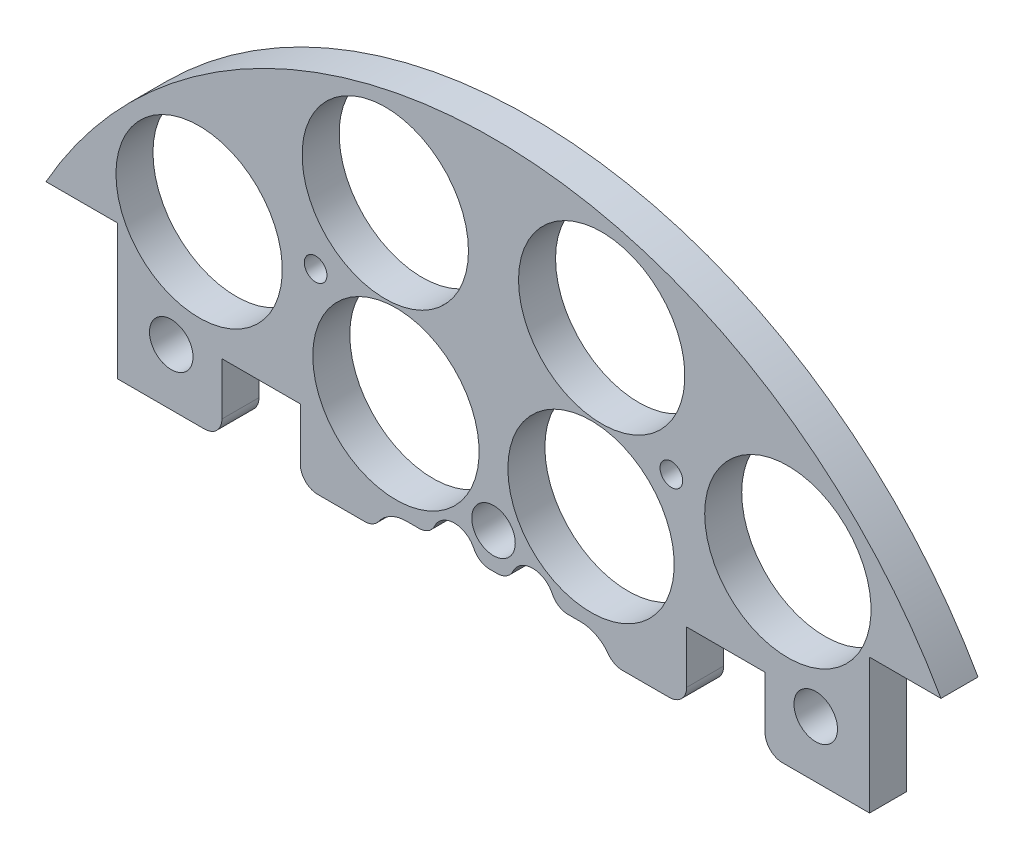
SolidWorks part; units mm, degrees
ref_plane "Front Plane" through (0, 0, 0) normal (0, 0, 1) x (1, 0, 0)
ref_plane "Top Plane" through (0, 0, 0) normal (0, 1, 0) x (1, 0, 0)
ref_plane "Right Plane" through (0, 0, 0) normal (1, 0, 0) x (0, 0, -1)
sketch "Sketch1" plane through (0, 0, 0) normal (0, 0, 1) x (1, 0, 0)
  line L0 (0, 0) -> (-82.1241, 0) construction
  line L1 (0, 0) -> (0, 95.6219) construction
  line L3 (-65.2538, 36.83) -> (-54.8398, 36.83)
  line L5 (-65.2538, -36.83) -> (-54.8398, -36.83)
  line L6 (-54.8398, 36.83) -> (-54.8398, -36.83)
  line L7 (65.2538, -36.83) -> (54.8398, -36.83)
  line L8 (65.2538, 36.83) -> (54.8398, 36.83)
  line L9 (54.8398, 36.83) -> (54.8398, -36.83)
  arc A0 (-65.2538, -36.83) -> (65.2538, -36.83) centre (0, 0) ccw
  circle A1 centre (-45.466, 11.049) radius 1.651
  circle A2 centre (-20.0673, 10.795) radius 1.651
  circle A3 centre (-20.0673, -10.795) radius 1.651
  circle A4 centre (-45.466, -11.049) radius 1.651
  circle A5 centre (45.466, -11.049) radius 1.651
  circle A6 centre (20.0673, -10.795) radius 1.651
  circle A7 centre (20.0673, 10.795) radius 1.651
  circle A8 centre (45.466, 11.049) radius 1.651
  arc A9 (65.2538, 36.83) -> (-65.2538, 36.83) centre (0, 0) ccw
  dimension "D2" = 3.302
  dimension "D3" = 3.302
  dimension "D4" = 25.4
  dimension "D5" = 10.795
  dimension "D10" = 45.466
  dimension "D6" = 73.66
  dimension "D7" = 10.414
  dimension "D8" = 74.93
  dimension "D9" = 74.93
  dimension "D11" = 36.83
extrude "Boss-Extrude2" add sketch "Sketch1" along normal blind 5.3975
sketch "Sketch2" plane through (0, 0, 5.3975) normal (0, 0, 1) x (1, 0, 0)
  line L0 (0, 68.58) -> (0, 55.88) construction
  line L1 (-9.525, 68.58) -> (9.525, 68.58)
  line L2 (-9.525, 68.58) -> (-9.525, 55.88)
  line L3 (-9.525, 55.88) -> (9.525, 55.88)
  line L4 (9.525, 68.58) -> (9.525, 55.88)
  line L5 (-9.525, 62.23) -> (9.525, 62.23) construction
  arc A0 (65.2538, 36.83) -> (-65.2538, 36.83) centre (0, 0) ccw construction
  circle A1 centre (-20.0673, 10.795) radius 1.651 construction
  circle A2 centre (20.0673, 10.795) radius 1.651 construction
  circle A3 centre (-6.731, 62.23) radius 1.143
  circle A4 centre (6.731, 62.23) radius 1.143
  dimension "D4" = 2.286
  dimension "D5" = 0
  dimension "D6" = 6.731
  dimension "D1" = 19.05
  dimension "D2" = 12.7
  dimension "D3" = 55.88
extrude "Cut-Extrude1" cut sketch "Sketch2" against normal through all contours A3 | A4
sketch "Sketch3" plane through (0, 0, 0) normal (0, 0, -1) x (-1, 0, 0)
  line L0 (0, 0) -> (0, -116.2908) construction
  line L1 (0, 0) -> (-153.8039, 0) construction
  circle A0 centre (-14.224, -56.7251) radius 12.1285
  circle A3 centre (14.224, -56.7251) radius 12.1285
  circle A4 centre (-42.926, -42.926) radius 12.1285
  circle A5 centre (14.224, 34.29) radius 12.1285
  circle A6 centre (-14.224, 34.29) radius 12.1285
  circle A8 centre (-42.926, 42.926) radius 12.1285
  circle A11 centre (42.926, 42.926) radius 12.1285
  circle A14 centre (42.926, -42.926) radius 12.1285
  point P36 (0, 0)
  point P53 (0, 0)
  point P55 (0, 0)
  dimension "D1" = 34.29
  dimension "D2" = 14.224
  dimension "D3" = 24.257
  dimension "D4" = 42.926
  dimension "D5" = 42.926
extrude "Cut-Extrude2" cut sketch "Sketch3" against normal through all
sketch "Sketch4" plane through (0, 0, 0) normal (0, 0, -1) x (-1, 0, 0)
  line L1 (-15.7702, 56.3138) -> (12.7925, 56.3138)
  line L2 (-15.7702, 56.3138) -> (-15.7702, 67.9913)
  line L3 (-15.7702, 67.9913) -> (12.7925, 67.9913)
  line L4 (12.7925, 56.3138) -> (12.7925, 67.9913)
extrude "Boss-Extrude3" add sketch "Sketch4" against normal up to surface (5.3975 mm away) up to face at (-55.0545, -42.926, 5.3975)
sketch "Sketch5" plane through (0, 0, 0) normal (0, 0, -1) x (-1, 0, 0)
  line L1 (-113.3786, -90.442) -> (117.3207, -90.442)
  line L2 (-113.3786, -90.442) -> (-113.3786, 17.145)
  line L3 (-113.3786, 17.145) -> (117.3207, 17.145)
  line L4 (117.3207, -90.442) -> (117.3207, 17.145)
  circle A1 centre (20.0673, 10.795) radius 1.651 construction
  dimension "D1" = 6.35
extrude "Cut-Extrude3" cut sketch "Sketch5" against normal through all
sketch "Sketch6" plane through (0, 0, 0) normal (0, 0, -1) x (-1, 0, 0)
  line L0 (0, 0) -> (0, 74.93) construction
  line L1 (0, 0) -> (-15.5068, 57.8721) construction
  arc A0 (65.2538, 36.83) -> (-65.2538, 36.83) centre (0, 0) ccw construction
  circle A1 centre (-15.7776, 58.8828) radius 12.1285
  circle A3 centre (15.7776, 58.8828) radius 12.1285
  dimension "D1" = 24.257
  dimension "D2" = 0
  dimension "D4" = 60.96
  dimension "D3" = 15
extrude "Cut-Extrude4" cut sketch "Sketch6" against normal through all
extrude "Cut-Extrude55" cut sketch "Sketch57" against normal through all both and the other way through all
sketch "Sketch57" plane through (-29.8755, 133.1307, 31.75) normal (0, 0, 1) x (0.01, 0.9999, 0)
  line L0 (-132.559, -31.3134) -> (-132.559, 57.8454) construction
  line L1 (-132.559, -31.3134) -> (-222.516, -31.3134) construction
  circle A0 centre (-157.959, 14.4066) radius 3.175
  circle A1 centre (-173.199, -31.3134) radius 3.175
  circle A3 centre (-157.959, -77.0334) radius 3.175
  circle A4 centre (-107.159, -77.0334) radius 3.175
  circle A5 centre (-91.919, -31.3134) radius 3.175
  circle A6 centre (-107.159, 14.4066) radius 3.175
sketch "Sketch58" [suppressed] plane through (0, 0, 0) normal (0, 0, -1) x (-1, 0, 0)
  circle A0 centre (-46.0825, 25.2068) radius 4.445
  circle A1 centre (-0.5172, 40.9032) radius 4.445
  circle A2 centre (45.3529, 26.1212) radius 4.445
  circle A3 centre (-46.0825, 25.2068) radius 3.175 construction
  circle A4 centre (-0.5172, 40.9032) radius 3.175 construction
  circle A5 centre (45.3529, 26.1212) radius 3.175 construction
  dimension "D1" = 1.27
  dimension "D2" = 1.27
  dimension "D3" = 1.27
extrude "Boss-Extrude4" [suppressed] add sketch "Sketch58" against normal up to surface (6.35 mm away)
extrude "Cut-Extrude56" cut sketch "Sketch59" against normal through all both and the other way through all
sketch "Sketch59" plane through (31.3134, 132.614, -19.05) normal (0, 0, -1) x (0, 1, 0)
  line L0 (-132.614, -31.3134) -> (-132.614, 57.8454) construction
  line L1 (-132.614, -31.3134) -> (-222.516, -31.3134) construction
  circle A0 centre (-158.014, 14.4066) radius 3.175
  circle A1 centre (-173.254, -31.3134) radius 3.175
  circle A3 centre (-158.014, -77.0334) radius 3.175
  circle A4 centre (-107.214, -77.0334) radius 3.175
  circle A5 centre (-91.974, -31.3134) radius 3.175
  circle A6 centre (-107.214, 14.4066) radius 3.175
extrude "Cut-Extrude60" cut sketch "Sketch63" against normal blind 29.21
sketch "Sketch63" plane through (31.3134, 132.614, -15.875) normal (0, 0, -1) x (0, 1, 0)
  line L0 (-132.559, -31.3134) -> (6.1626, -31.3134) construction
  line L2 (-132.559, -31.3134) -> (-132.559, -122.6589) construction
  circle A0 centre (-190.979, 2.9766) radius 1.651
  circle A2 centre (-154.784, -31.3134) radius 1.651
  circle A3 centre (-190.979, -65.6034) radius 1.651
  circle A4 centre (-110.334, -31.3134) radius 1.651
  circle A5 centre (-74.139, -65.6034) radius 1.651
  circle A6 centre (-74.139, 2.9766) radius 1.651
extrude "Cut-Extrude158" cut sketch "Sketch161" against normal blind 29.21
sketch "Sketch161" plane through (-31.3134, 132.559, 6.35) normal (0, 0, 1) x (0, 1, 0)
  line L0 (-143.7712, -34.3645) -> (6.1626, -34.3645) construction
  line L2 (-143.7712, -34.3645) -> (-143.7712, -122.6589) construction
  circle A0 centre (-202.1912, -0.0745) radius 1.651
  circle A2 centre (-165.9962, -34.3645) radius 1.651
  circle A3 centre (-202.1912, -68.6545) radius 1.651
  circle A4 centre (-121.5462, -34.3645) radius 1.651
  circle A5 centre (-85.3512, -68.6545) radius 1.651
  circle A6 centre (-85.3512, -0.0745) radius 1.651
sketch "Sketch162" plane through (0, 0, 5.3975) normal (0, 0, 1) x (1, 0, 0)
  line L0 (-54.8398, 17.145) -> (54.8398, 17.145) construction
  line L1 (39.5998, 17.145) -> (28.1698, 17.145)
  line L2 (39.5998, 17.145) -> (39.5998, 27.305)
  line L3 (39.5998, 27.305) -> (28.1698, 27.305)
  line L4 (28.1698, 17.145) -> (28.1698, 27.305)
  line L5 (0, -4.3124) -> (0, 89.5869) construction
  line L6 (-28.1698, 17.145) -> (-39.5998, 17.145)
  line L7 (-28.1698, 17.145) -> (-28.1698, 27.305)
  line L8 (-28.1698, 27.305) -> (-39.5998, 27.305)
  line L9 (-39.5998, 17.145) -> (-39.5998, 27.305)
  line L10 (54.8398, 17.145) -> (54.8398, 36.83) construction
  dimension "D1" = 10.16
  dimension "D2" = 11.43
  dimension "D3" = 15.24
extrude "Cut-Extrude159" cut sketch "Sketch162" against normal through all
extrude "Cut-Extrude215" cut sketch "Sketch218" against normal blind 97.79
sketch "Sketch218" plane through (30.092, 4.0835, -10.795) normal (0, 0, -1) x (-1, 0, 0)
  line L0 (30.092, -29.4835) -> (30.092, 6.2385) construction
  circle A0 centre (4.1544, -49.7288) radius 1.651
  circle A4 centre (56.0296, -49.7288) radius 1.651
  circle A5 centre (4.1544, 41.3825) radius 1.651
  circle A9 centre (56.0296, 41.3825) radius 1.651
extrude "Cut-Extrude269" cut sketch "Sketch272" against normal blind 48.768 and the other way blind 103.378
sketch "Sketch272" plane through (30.092, 4.0835, 25.3365) normal (0, 0, -1) x (-1, 0, 0)
  line L0 (30.092, -4.0835) -> (148.6336, -4.0835) construction
  line L1 (30.092, -4.0835) -> (30.092, 90.452) construction
  circle A0 centre (-16.898, 21.3165) radius 3.175
  circle A1 centre (77.082, 21.3165) radius 3.175
  circle A2 centre (30.092, 21.3165) radius 3.175
  circle A4 centre (77.082, -29.4835) radius 3.175
  circle A5 centre (30.092, -29.4835) radius 3.175
  circle A6 centre (-16.898, -29.4835) radius 3.175
sketch "Sketch165" plane through (0, 0, 0) normal (0, 0, -1) x (-1, 0, 0)
  line L0 (0, 0) -> (0, 12.9674) construction
  line L1 (12.7, 20.24) -> (8.889, 20.24)
  line L2 (7.7, 15.24) -> (-7.7, 15.24)
  line L3 (2.541, 20.24) -> (-2.541, 20.24)
  line L4 (-8.889, 20.24) -> (-12.7, 20.24)
  arc A0 (7.7, 15.24) -> (12.7, 20.24) centre (12.7, 15.24) ccw
  arc A1 (-7.7, 15.24) -> (-12.7, 20.24) centre (-12.7, 15.24) cw
  arc A2 (8.889, 20.24) -> (2.541, 20.24) centre (5.715, 20.32) ccw
  arc A3 (-2.541, 20.24) -> (-8.889, 20.24) centre (-5.715, 20.32) ccw
  dimension "D1" = 10
  dimension "D4" = 6.35
  dimension "D5" = 6.35
  dimension "D2" = 15.24
  dimension "D3" = 12.7
  dimension "D6" = 11.43
  dimension "D7" = 5.715
  dimension "D8" = 20.32
extrude "Cut-Extrude162" cut sketch "Sketch165" against normal blind 30.48
fillet "Fillet1" radius 2.54 10 edges at (39.5998, 17.145, 2.6987) (28.1698, 17.145, 2.6987) (17.3229, 17.145, 2.6987) (8.889, 20.24, 2.6987) (-2.541, 20.24, 2.6987) (2.541, 20.24, 2.6987) (-8.889, 20.24, 2.6987) (-17.3229, 17.145, 2.6987) (-28.1698, 17.145, 2.6987) (-39.5998, 17.145, 2.6987)
